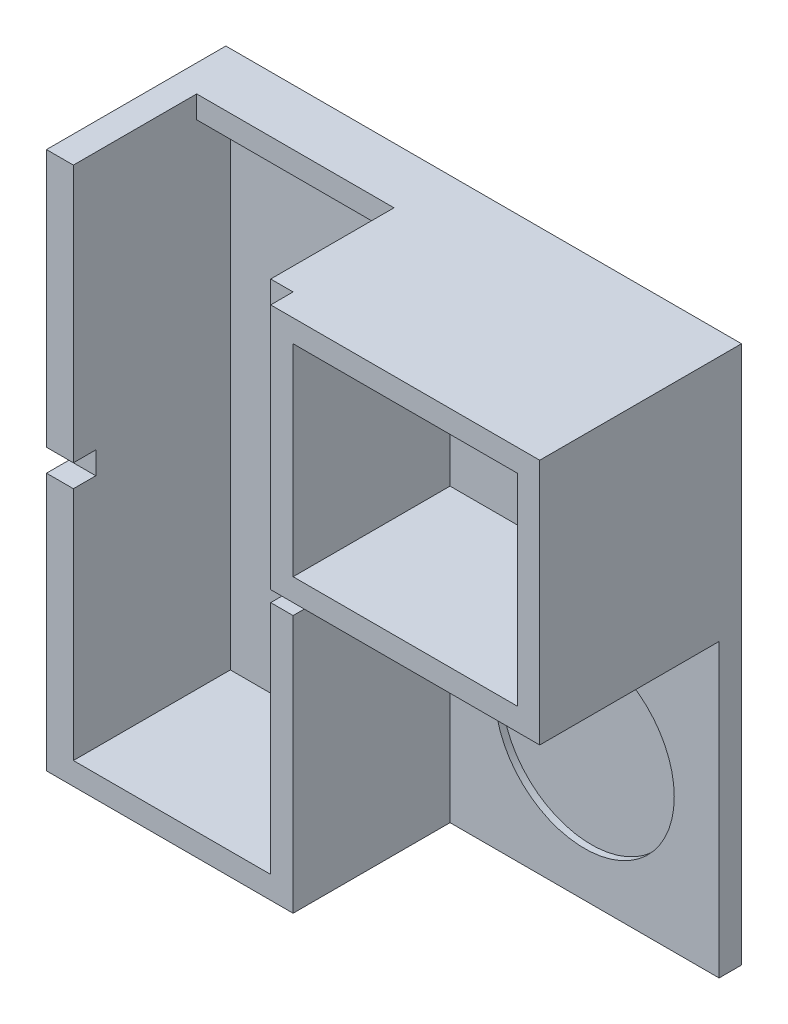
SolidWorks part; units mm, degrees
ref_plane "Plano frontal" through (0, 0, 0) normal (0, 0, 1) x (1, 0, 0)
ref_plane "Plano superior" through (0, 0, 0) normal (0, 1, 0) x (1, 0, 0)
ref_plane "Plano direito" through (0, 0, 0) normal (1, 0, 0) x (0, 0, -1)
sketch "Esboço1" plane through (0, 0, 0) normal (0, 0, 1) x (1, 0, 0)
  line L3 (-99.2177, 25.0239) -> (70.7823, 25.0239)
  line L4 (70.7823, 0) -> (70.7823, 25.0239)
  line L7 (-99.2177, 25.0239) -> (-269.2177, 25.0239)
  line L8 (-269.2177, 0) -> (-269.2177, 25.0239)
  line L11 (-99.2177, -214.9761) -> (-269.2177, -214.9761)
  line L12 (-269.2177, 0) -> (-269.2177, -214.9761)
  line L15 (-99.2177, -214.9761) -> (70.7823, -214.9761)
  line L16 (70.7823, 0) -> (70.7823, -214.9761)
  dimension "D1" = 340
  dimension "D2" = 240
extrude "Ressalto-extrusão1" add sketch "Esboço1" along normal blind 10 contours L7 L8 L12 L11 L15 L16 L4 L3
sketch "Esboço2" plane through (0, 0, 10) normal (0, 0, 1) x (1, 0, 0)
  line L8 (-49.2177, -214.9761) -> (-269.2177, -214.9761)
  line L9 (-49.2177, -214.9761) -> (-49.2177, -204.9761)
  line L10 (-49.2177, -204.9761) -> (-269.2177, -204.9761)
  line L11 (-269.2177, -214.9761) -> (-269.2177, -204.9761)
  line L12 (-269.2177, 25.0239) -> (-269.2177, -214.9761) construction
  line L13 (-269.2177, -214.9761) -> (70.7823, -214.9761) construction
  line L14 (-269.2177, 25.0239) -> (70.7823, 25.0239) construction
  line L15 (-49.2177, 25.0239) -> (-269.2177, 25.0239)
  line L16 (-49.2177, 25.0239) -> (-49.2177, 15.0239)
  line L17 (-49.2177, 15.0239) -> (-269.2177, 15.0239)
  line L18 (-269.2177, 25.0239) -> (-269.2177, 15.0239)
  line L20 (-49.2177, 15.0239) -> (-59.2177, 15.0239)
  line L21 (-49.2177, 15.0239) -> (-49.2177, -214.9761)
  line L22 (-49.2177, -214.9761) -> (-59.2177, -214.9761)
  line L23 (-59.2177, 15.0239) -> (-59.2177, -214.9761)
  dimension "D3" = 220
  dimension "D4" = 10
  dimension "D5" = 10
  dimension "D6" = 10
extrude "Ressalto-extrusão4" add sketch "Esboço2" along normal blind 70 contours L8 L11 L10 L9 | L16 L15 L18 L17 | L20 L23 L22 L21
sketch "Esboço7" plane through (0, 0, 10) normal (0, 0, 1) x (1, 0, 0)
  line L0 (70.7823, -214.9761) -> (70.7823, 25.0239) construction
  line L1 (10.7823, -214.9761) -> (10.7823, -154.9761)
  line L3 (-49.2177, -214.9761) -> (-49.2177, 25.0239) construction
  line L4 (-49.2177, -214.9761) -> (70.7823, -214.9761) construction
  line L5 (70.7823, -84.9761) -> (-49.2177, -84.9761)
  line L7 (70.7823, -84.9761) -> (70.7823, -74.9761)
  line L8 (70.7823, -74.9761) -> (-49.2177, -74.9761)
  line L9 (-49.2177, -84.9761) -> (-49.2177, -74.9761)
  circle A0 centre (10.7823, -154.9761) radius 40
  dimension "D2" = 80
  dimension "D1" = 60
  dimension "D3" = 60
  dimension "D4" = 70
  dimension "D5" = 10
extrude "Corte-extrusão1" cut sketch "Esboço7" against normal blind 3 contours A0
sketch "Esboço21" plane through (0, 25.0239, 0) normal (0, 1, 0) x (1, 0, 0)
  line L0 (-269.2177, -80) -> (-269.2177, 0) construction
  line L1 (-259.2177, -25) -> (-59.2177, -25)
  line L2 (-259.2177, -25) -> (-259.2177, -70)
  line L3 (-259.2177, -70) -> (-59.2177, -70)
  line L4 (-59.2177, -25) -> (-59.2177, -70)
  line L5 (-49.2177, -80) -> (-269.2177, -80) construction
  line L6 (70.7823, 0) -> (-269.2177, 0) construction
  dimension "D1" = 10
  dimension "D2" = 10
  dimension "D3" = 25
  dimension "D4" = 200
extrude "Corte-extrusão5" cut sketch "Esboço21" against normal blind 100 contours L1 L4 L3 L2
sketch "Esboço28" plane through (0, 0, 10) normal (0, 0, 1) x (1, 0, 0)
  line L0 (-49.2177, -214.9761) -> (-49.2177, 25.0239) construction
  line L2 (70.7823, -84.9761) -> (70.7823, 25.0239)
  line L3 (70.7823, -84.9761) -> (-49.2177, -84.9761)
  line L4 (-49.2177, -74.9761) -> (-49.2177, -84.9761)
  line L6 (-49.2177, 25.0239) -> (70.7823, 25.0239) construction
  line L9 (70.7823, 25.0239) -> (60.7823, 25.0239)
  line L13 (-49.2177, -74.9761) -> (-49.2177, 25.0239)
  line L14 (-49.2177, 25.0239) -> (-39.2177, 25.0239)
  line L16 (-39.2177, 25.0239) -> (60.7823, 25.0239)
  circle A0 centre (10.7823, -154.9761) radius 40 construction
  dimension "D2" = 70
extrude "Ressalto-extrusão5" add sketch "Esboço28" along normal blind 80 contours L2 L9 L16 L14 L13 L4 L3
sketch "Esboço29" plane through (0, -214.9761, 0) normal (0, -1, 0) x (1, 0, 0)
  line L0 (-49.2177, 80) -> (-269.2177, 80) construction
  line L1 (-269.2177, 80) -> (-159.2177, 80)
  line L2 (-269.2177, 80) -> (-269.2177, 0)
  line L3 (-269.2177, 0) -> (-159.2177, 0)
  line L4 (-159.2177, 80) -> (-159.2177, 0)
  line L5 (70.7823, 0) -> (-269.2177, 0) construction
  dimension "D1" = 110
extrude "Corte-extrusão8" cut sketch "Esboço29" against normal blind 250
sketch "Esboço30" plane through (0, 0, 25) normal (0, 0, 1) x (1, 0, 0)
  line L0 (-159.2177, 15.0239) -> (-159.2177, 25.0239) construction
  line L1 (-159.2177, 25.0239) -> (-147.2177, 25.0239)
  line L2 (-159.2177, 25.0239) -> (-159.2177, 15.0239)
  line L3 (-159.2177, 15.0239) -> (-147.2177, 15.0239)
  line L4 (-147.2177, 25.0239) -> (-147.2177, 15.0239)
  line L5 (-59.2177, 15.0239) -> (-159.2177, 15.0239) construction
  dimension "D1" = 12
extrude "Ressalto-extrusão6" add sketch "Esboço30" along normal blind 50
sketch "Esboço31" plane through (0, 0, 90) normal (0, 0, 1) x (1, 0, 0)
  line L0 (70.7823, -84.9761) -> (70.7823, 25.0239) construction
  line L1 (60.7823, 15.0239) -> (-39.2177, 15.0239)
  line L2 (60.7823, 15.0239) -> (60.7823, -74.9761)
  line L3 (60.7823, -74.9761) -> (-39.2177, -74.9761)
  line L4 (-39.2177, 15.0239) -> (-39.2177, -74.9761)
  line L5 (70.7823, -84.9761) -> (-49.2177, -84.9761) construction
  line L7 (-49.2177, 25.0239) -> (70.7823, 25.0239) construction
  line L8 (-59.2177, 15.0239) -> (-59.2177, -204.9761) construction
  point P6 (10.7823, -84.9761)
  dimension "D1" = 10
  dimension "D2" = 10
  dimension "D3" = 20
  dimension "D4" = 10
extrude "Corte-extrusão9" cut sketch "Esboço31" against normal blind 70
sketch "Esboço38" plane through (0, 15.0239, 0) normal (0, -1, 0) x (1, 0, 0)
  line L0 (-59.2177, 80) -> (-159.2177, 80) construction
  line L1 (-147.2177, 80) -> (-159.2177, 80)
  line L2 (-147.2177, 80) -> (-147.2177, 10)
  line L3 (-147.2177, 10) -> (-159.2177, 10)
  line L4 (-159.2177, 80) -> (-159.2177, 10)
  line L5 (-59.2177, 10) -> (-159.2177, 10) construction
extrude "Ressalto-extrusão8" add sketch "Esboço38" along normal blind 220
sketch "Esboço39" plane through (0, 0, 80) normal (0, 0, 1) x (1, 0, 0)
  line L0 (-59.2177, 15.0239) -> (-59.2177, -204.9761) construction
  line L1 (-59.2177, -99.9761) -> (-49.2177, -99.9761)
  line L2 (-59.2177, -99.9761) -> (-59.2177, -89.9761)
  line L3 (-59.2177, -89.9761) -> (-49.2177, -89.9761)
  line L4 (-49.2177, -99.9761) -> (-49.2177, -89.9761)
  line L5 (-49.2177, -214.9761) -> (-49.2177, -84.9761) construction
  line L6 (-147.2177, -204.9761) -> (-147.2177, 15.0239) construction
  line L7 (-147.2177, -89.9761) -> (-159.2177, -89.9761)
  line L8 (-147.2177, -89.9761) -> (-147.2177, -99.9761)
  line L9 (-147.2177, -99.9761) -> (-159.2177, -99.9761)
  line L10 (-159.2177, -89.9761) -> (-159.2177, -99.9761)
  line L11 (-159.2177, 25.0239) -> (-159.2177, -214.9761) construction
  line L12 (-49.2177, -214.9761) -> (-159.2177, -214.9761) construction
  line L13 (-49.2177, 25.0239) -> (-159.2177, 25.0239) construction
  dimension "D1" = 115
  dimension "D2" = 115
extrude "Corte-extrusão10" cut sketch "Esboço39" against normal blind 10
sketch "Esboço40" plane through (0, 25.0239, 0) normal (0, 1, 0) x (1, 0, 0)
  line L0 (-147.2177, -70) -> (-147.2177, -25) construction
  line L1 (-59.2177, -70) -> (-147.2177, -70)
  line L2 (-59.2177, -70) -> (-59.2177, -80)
  line L3 (-59.2177, -80) -> (-147.2177, -80)
  line L4 (-147.2177, -70) -> (-147.2177, -80)
extrude "Corte-extrusão11" cut sketch "Esboço40" against normal blind 10 contours L2 L3 L4 L1
